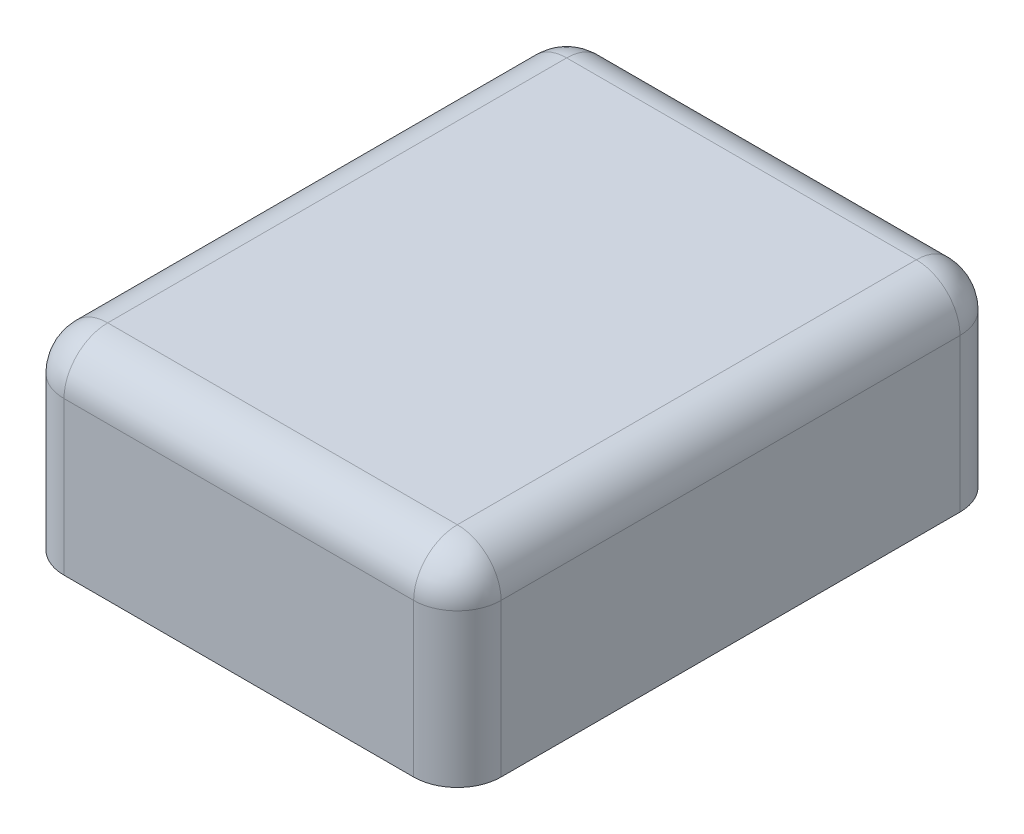
SolidWorks part; units mm, degrees
ref_plane "Front Plane" through (0, 0, 0) normal (0, 0, 1) x (1, 0, 0)
ref_plane "Top Plane" through (0, 0, 0) normal (0, 1, 0) x (1, 0, 0)
ref_plane "Right Plane" through (0, 0, 0) normal (1, 0, 0) x (0, 0, -1)
sketch "BaseS" plane through (0, 0, 0) normal (0, 1, 0) x (1, 0, 0)
  line L1 (-1, 1.25) -> (1, 1.25)
  line L2 (-1, 1.25) -> (-1, -1.25)
  line L3 (-1, -1.25) -> (1, -1.25)
  line L4 (1, 1.25) -> (1, -1.25)
  line L5 (-1, 1.25) -> (1, -1.25) construction
  line L6 (-1, -1.25) -> (1, 1.25) construction
  point P0 (0, 0)
  dimension "Width" = 2
  dimension "Length" = 2.5
extrude "Base" add sketch "BaseS" along normal blind 0.9
fillet "SideF" radius 0.2 4 edges at (1, 0.45, 1.25) (1, 0.45, -1.25) (-1, 0.45, 1.25) (-1, 0.45, -1.25)
fillet "TopF" radius 0.2 8 edges at (-0.9414, 0.9, 1.1914) (-1, 0.9, 0) (-0.9414, 0.9, -1.1914) (0, 0.9, -1.25) (0.9414, 0.9, -1.1914) (1, 0.9, 0) (0.9414, 0.9, 1.1914) (0, 0.9, 1.25)
